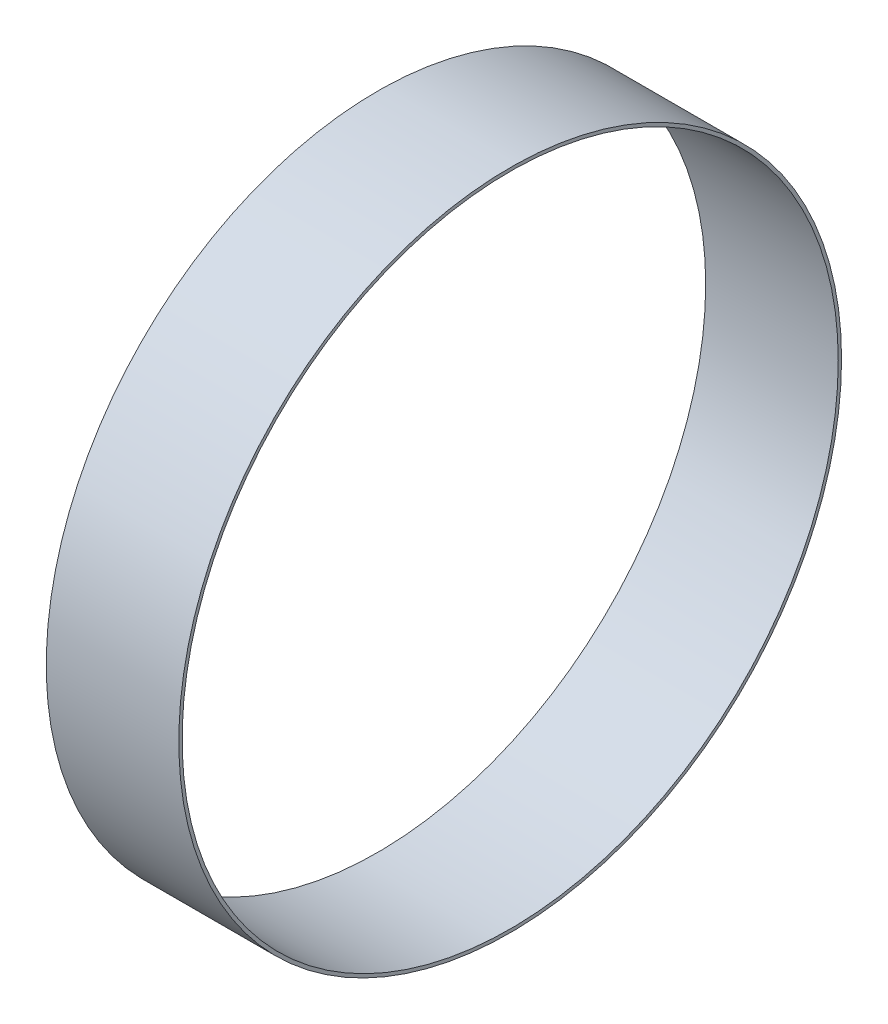
SolidWorks part; units mm, degrees
material "Elastic Band"
ref_plane "Front Plane" through (0, 0, 0) normal (0, 0, 1) x (1, 0, 0)
ref_plane "Top Plane" through (0, 0, 0) normal (0, 1, 0) x (1, 0, 0)
ref_plane "Right Plane" through (0, 0, 0) normal (1, 0, 0) x (0, 0, -1)
sketch "Sketch1" plane through (0, 0, 0) normal (1, 0, 0) x (0, 0, -1)
  circle A0 centre (0, 0) radius 49.5
  circle A1 centre (0, 0) radius 50
  dimension "D1" = 100
  dimension "D2" = 99
extrude "Boss-Extrude1" add sketch "Sketch1" along normal blind 20
